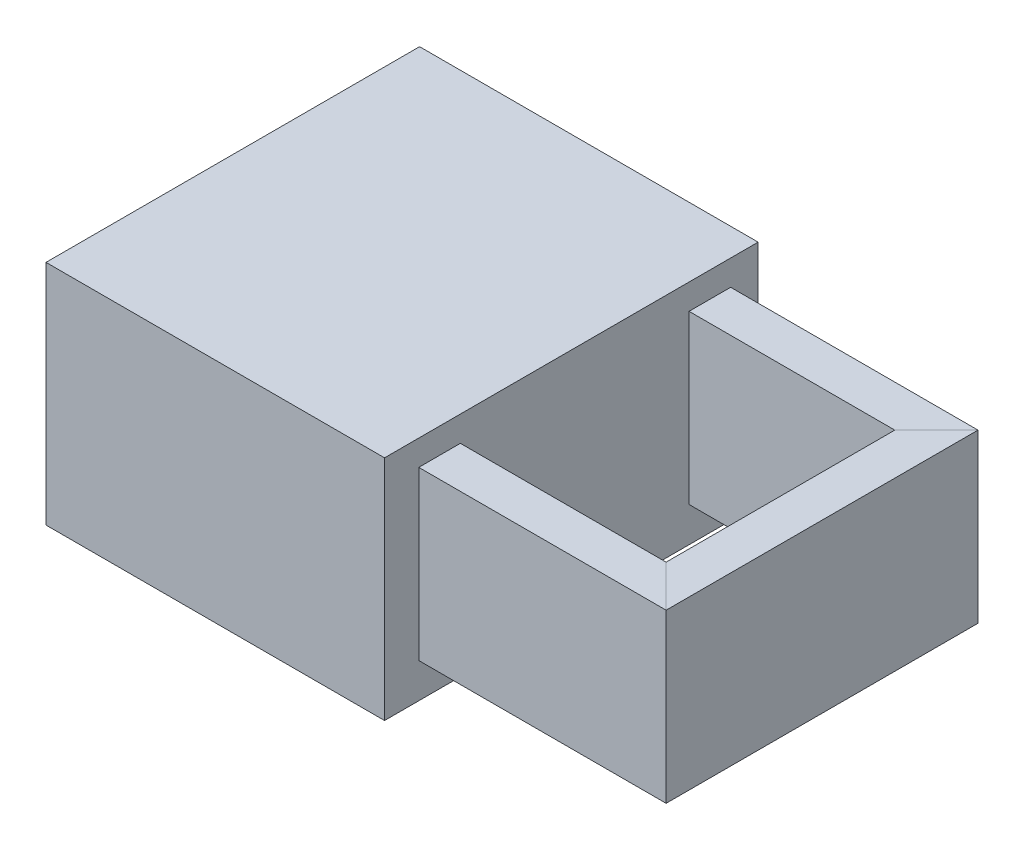
SolidWorks part; units mm, degrees
ref_plane "Front Plane" through (0, 0, 0) normal (0, 0, 1) x (1, 0, 0)
ref_plane "Top Plane" through (0, 0, 0) normal (0, 1, 0) x (1, 0, 0)
ref_plane "Right Plane" through (0, 0, 0) normal (1, 0, 0) x (0, 0, -1)
sketch "Sketch1" plane through (-20.3187, -25.3134, 0) normal (0, 0, 1) x (1, 0, 0)
  line L1 (-26.1755, 21.3387) -> (55.3859, 21.3387)
  line L2 (-26.1755, 21.3387) -> (-26.1755, -33.4781)
  line L3 (-26.1755, -33.4781) -> (55.3859, -33.4781)
  line L4 (55.3859, 21.3387) -> (55.3859, -33.4781)
extrude "Boss-Extrude1" add sketch "Sketch1" along normal blind 90 contours L1 L4 L3 L2
sketch "Sketch2" plane through (35.0672, 0, 0) normal (1, 0, 0) x (0, 0, -1)
  line L1 (-81.7562, -10.0879) -> (-71.7364, -10.0879)
  line L2 (-81.7562, -10.0879) -> (-81.7562, -50.3889)
  line L3 (-81.7562, -50.3889) -> (-71.7364, -50.3889)
  line L4 (-71.7364, -10.0879) -> (-71.7364, -50.3889)
ref_plane "Plane1" through (0, -10.0879, 0) normal (0, 1, 0) x (1, 0, 0)
sketch "Sketch3" plane through (0, -10.0879, 0) normal (0, 1, 0) x (1, 0, 0)
  line L0 (35.0672, -76.7463) -> (89.648, -76.7463)
  line L1 (35.0672, -81.7562) -> (35.0672, -71.7364) construction
  line L2 (89.648, -76.7463) -> (89.648, -11.6321)
  line L3 (89.648, -11.6321) -> (35.0672, -11.6321)
sweep "Sweep3" add profiles "Sketch2" path "Sketch3"
